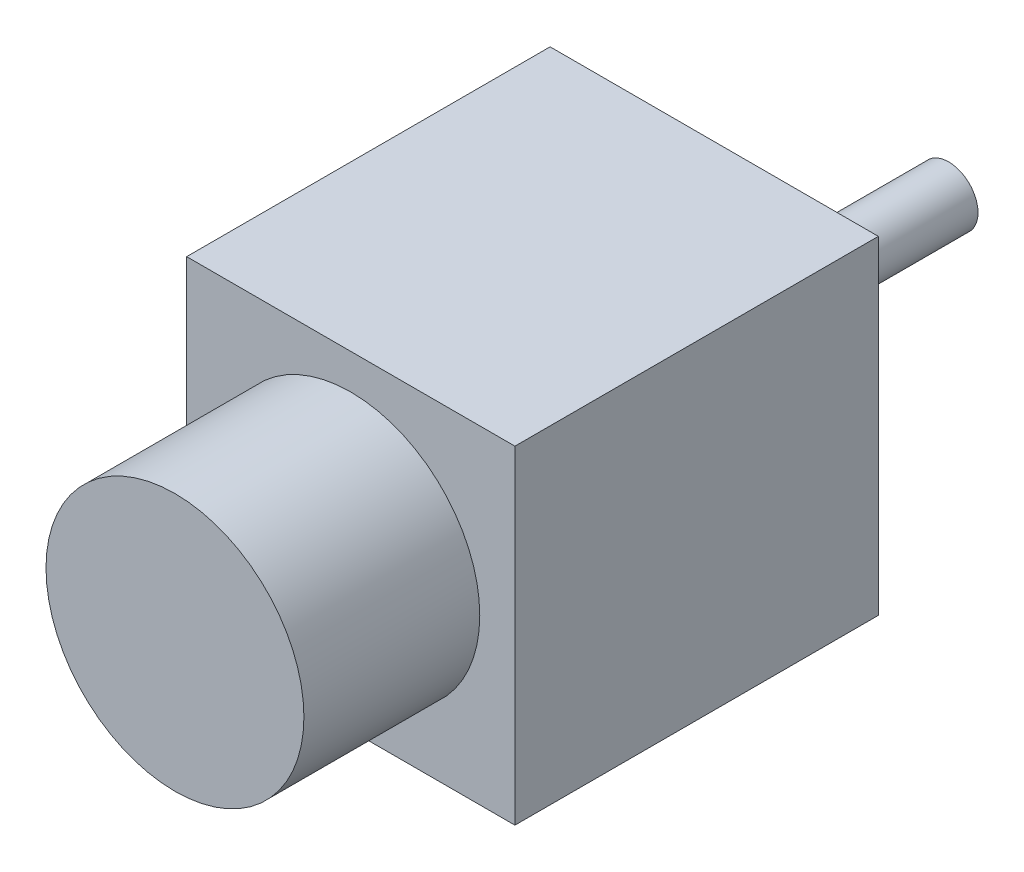
SolidWorks part; units mm, degrees
ref_plane "Front Plane" through (0, 0, 0) normal (0, 0, 1) x (1, 0, 0)
ref_plane "Top Plane" through (0, 0, 0) normal (0, 1, 0) x (1, 0, 0)
ref_plane "Right Plane" through (0, 0, 0) normal (1, 0, 0) x (0, 0, -1)
sketch "Sketch1" plane through (0, 0, 0) normal (0, 0, 1) x (1, 0, 0)
  line L5 (0, 0) -> (28, 0)
  line L6 (0, 0) -> (0, -28)
  line L7 (0, -28) -> (28, -28)
  line L8 (28, 0) -> (28, -28)
  dimension "D1" = 28
  dimension "D2" = 28
extrude "Boss-Extrude1" add sketch "Sketch1" along normal blind 46
sketch "Sketch2" plane through (0, 0, 46) normal (0, 0, 1) x (1, 0, 0)
  line L4 (0, 0) -> (0, -28)
  line L5 (0, -28) -> (28, -28)
  line L6 (28, -28) -> (28, 0)
  line L7 (28, 0) -> (0, 0)
  line L8 (0, 0) -> (0, -28)
  line L9 (0, -28) -> (28, -28)
  line L10 (28, -28) -> (28, 0)
  line L11 (28, 0) -> (0, 0)
  circle A0 centre (14, -14) radius 11
  point P2 (0, 0)
  point P5 (0, 0)
  point P7 (0, -14)
  point P9 (14, 0)
  dimension "D2" = 22
  dimension "D1" = 0
extrude "Cut-Extrude1" cut sketch "Sketch2" against normal blind 15
sketch "Sketch3" plane through (0, 0, 0) normal (0, 0, -1) x (-1, 0, 0)
  line L4 (0, -28) -> (0, 0)
  line L5 (0, 0) -> (-28, 0)
  line L6 (-28, 0) -> (-28, -28)
  line L7 (-28, -28) -> (0, -28)
  line L8 (0, -28) -> (0, 0)
  line L9 (0, 0) -> (-28, 0)
  line L10 (-28, 0) -> (-28, -28)
  line L11 (-28, -28) -> (0, -28)
  circle A0 centre (-14, -14) radius 2.5
  point P2 (0, 0)
  point P5 (0, 0)
  point P7 (-14, 0)
  point P9 (0, 0)
  point P10 (-28, -14)
  dimension "D2" = 5
  dimension "D1" = 0
extrude "Boss-Extrude2" add sketch "Sketch3" along normal blind 20 contours A0
